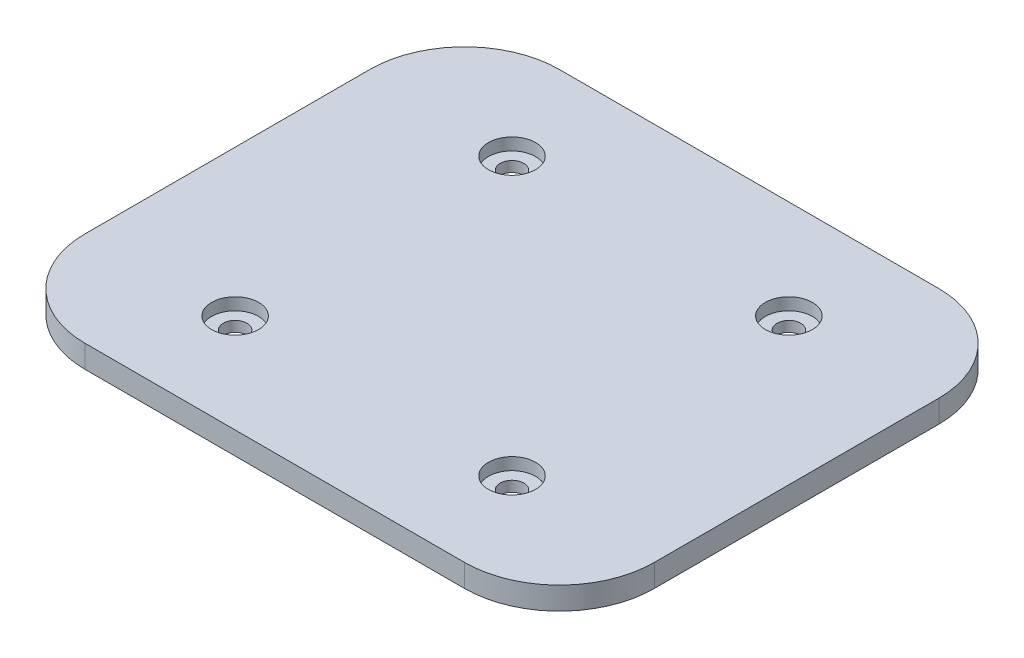
SolidWorks part; units mm, degrees
material "1060 Alloy"
ref_plane "Front" through (0, 0, 0) normal (0, 0, 1) x (1, 0, 0)
ref_plane "Top" through (0, 0, 0) normal (0, 1, 0) x (1, 0, 0)
ref_plane "Right" through (0, 0, 0) normal (1, 0, 0) x (0, 0, -1)
sketch "Sketch1" plane through (0, 0, 0) normal (0, 1, 0) x (1, 0, 0)
  line L1 (40, -50) -> (-40, -50)
  line L2 (60, -30) -> (60, 30)
  line L3 (40, 50) -> (-40, 50)
  line L4 (-60, -30) -> (-60, 30)
  line L5 (60, -50) -> (-60, 50) construction
  line L6 (60, 50) -> (-60, -50) construction
  arc A1 (-40, -50) -> (-60, -30) centre (-40, -30) cw
  arc A2 (40, -50) -> (60, -30) centre (40, -30) ccw
  arc A3 (60, 30) -> (40, 50) centre (40, 30) ccw
  arc A4 (-40, 50) -> (-60, 30) centre (-40, 30) ccw
  point P0 (0, 50)
  dimension "D1" = 100
  dimension "D2" = 20
  dimension "D3" = 120
extrude "Boss-Extrude1" add sketch "Sketch1" along normal blind 4.7625
hole_wizard "CBORE for #10 Button Head Cap Screw1" positions "Sketch2" profile "Sketch3" counterbore size "#10" standard "ANSI Inch" end condition through all
sketch "Sketch2" plane through (0, 4.7625, 0) normal (0, 1, 0) x (1, 0, 0)
  line L0 (-29.1858, -29.1858) -> (29.1858, 29.1858) construction
  line L2 (0, 41.275) -> (0, -41.275) construction
  circle A0 centre (0, 0) radius 41.275 construction
  point P0 (29.1858, 29.1858)
  point P6 (29.1858, -29.1858)
  point P7 (-29.1858, -29.1858)
  point P8 (-29.1858, 29.1858)
  dimension "D2" = 82.55
  dimension "D3" = 45
  dimension "D1" = 4
sketch "Sketch3" plane through (29.1858, 4.7625, -29.1858) normal (1, 0, 0) x (0, 0, 1)
  line L0 (0, 0) -> (0, 4.7625)
  line L1 (0, 4.7625) -> (2.4892, 4.7625)
  line L3 (2.4892, 4.7625) -> (2.4892, 2.5654)
  line L4 (2.4892, 2.5654) -> (4.9606, 2.5654)
  line L5 (4.9606, 2.5654) -> (4.9606, 0)
  line L7 (4.9606, 0) -> (0, 0)
  line L11 (0, -6.35) -> (0, 107.95) construction
  dimension "Thru Hole Dia." = 4.9784
  dimension "Thru Hole Depth" = 4.7625
  dimension "C'Bore Dia." = 9.9212
  dimension "C'Bore Depth" = 2.5654
sketch "Sketch5" plane through (0, 4.7625, 0) normal (0, 1, 0) x (1, 0, 0)
  line L0 (-49.7625, 50) -> (-49.7625, -50)
  line L1 (40, 50) -> (-40, 50) construction
  line L2 (-40, -50) -> (40, -50) construction
  line L3 (49.7625, -50) -> (49.7625, 50)
  line L4 (-49.7625, 0) -> (49.7625, 0) construction
  dimension "D1" = 99.525
